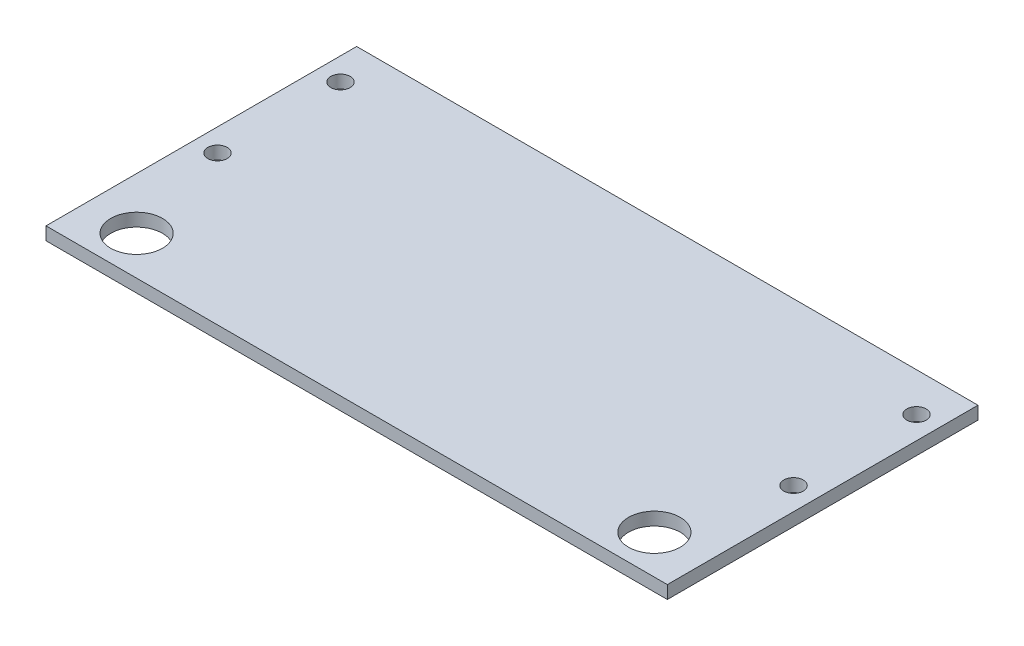
SolidWorks part; units mm, degrees
ref_plane "Front Plane" through (0, 0, 0) normal (0, 0, 1) x (1, 0, 0)
ref_plane "Top Plane" through (0, 0, 0) normal (0, 1, 0) x (1, 0, 0)
ref_plane "Right Plane" through (0, 0, 0) normal (1, 0, 0) x (0, 0, -1)
sketch "Sketch1" plane through (0, 0, 0) normal (0, 1, 0) x (1, 0, 0)
  line L1 (0, 0) -> (304.8, 0)
  line L2 (0, 0) -> (0, 152.4)
  line L3 (0, 152.4) -> (304.8, 152.4)
  line L4 (304.8, 0) -> (304.8, 152.4)
  dimension "D1" = 152.4
  dimension "D2" = 304.8
extrude "Boss-Extrude1" add sketch "Sketch1" along normal blind 6.35
sketch "Sketch2" plane through (0, 6.35, 0) normal (0, 1, 0) x (-1, 0, 0)
  line L0 (-152.4, -152.4) -> (-152.4, 0) construction
  line L1 (-304.8, -152.4) -> (0, -152.4) construction
  line L2 (0, 0) -> (-304.8, 0) construction
  line L3 (0, -152.4) -> (0, 0) construction
  line L4 (-11.1125, -133.35) -> (-11.1125, -73.025) construction
  circle A0 centre (-25.4, -19.05) radius 12.7
  circle A1 centre (-293.6875, -133.35) radius 4.7625
  circle A2 centre (-11.1125, -133.35) radius 4.7625
  circle A3 centre (-11.1125, -73.025) radius 4.7625
  circle A4 centre (-293.6875, -73.025) radius 4.7625
  circle A5 centre (-279.4, -19.05) radius 12.7
  dimension "D1" = 25.4
  dimension "D5" = 9.525
  dimension "D2" = 25.4
  dimension "D3" = 19.05
  dimension "D4" = 60.325
  dimension "D6" = 19.05
  dimension "D7" = 141.2875
extrude "Cut-Extrude1" cut sketch "Sketch2" against normal up to next
